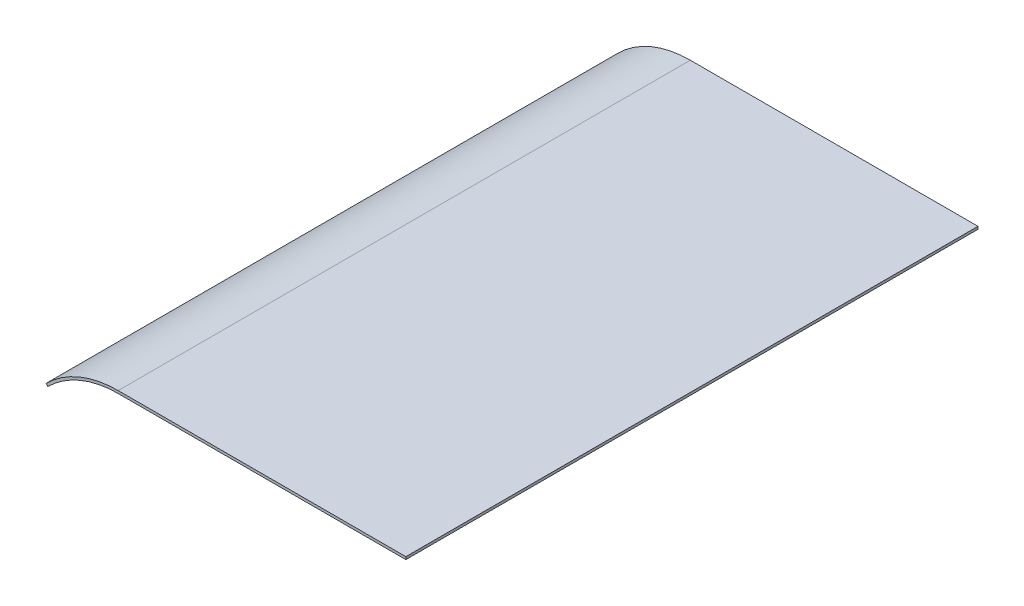
SolidWorks part; units mm, degrees
ref_plane "Front Plane" through (0, 0, 0) normal (0, 0, 1) x (1, 0, 0)
ref_plane "Top Plane" through (0, 0, 0) normal (0, 1, 0) x (1, 0, 0)
ref_plane "Right Plane" through (0, 0, 0) normal (1, 0, 0) x (0, 0, -1)
sketch "Sketch1" plane through (0, 0, 0) normal (0, 0, 1) x (1, 0, 0)
  line L0 (-418.175, 963.93) -> (-584.2, 963.93)
  line L1 (-415, 963.93) -> (-529.5466, 963.93) construction
  line L2 (-415, 963.93) -> (-415, 813.93) construction
  circle A0 centre (-584.2, 905.0248) radius 55.753 construction
  circle A1 centre (-584.2, 905.0248) radius 55.753 construction
  arc A2 (-584.2, 963.93) -> (-625.8522, 946.6771) centre (-584.2, 905.0248) ccw
  dimension "D1" = 3.175
  dimension "D2" = 45
extrude "Extrude-Thin1" add sketch "Sketch1" along normal mid plane 330.2 thin thin type one direction reverse wall 1.5
